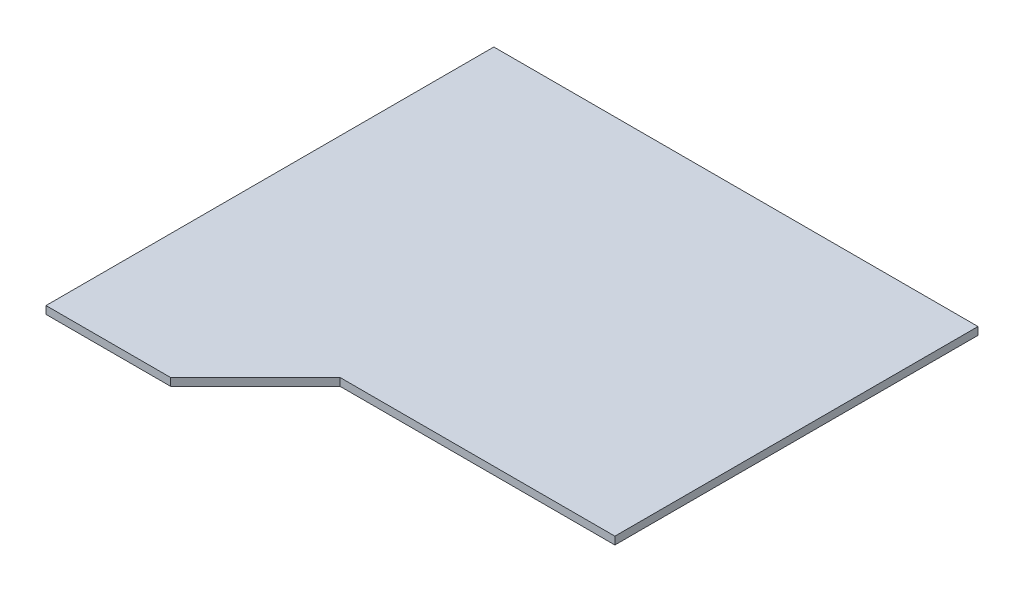
SolidWorks part; units mm, degrees
ref_plane "Front Plane" through (0, 0, 0) normal (0, 0, 1) x (1, 0, 0)
ref_plane "Top Plane" through (0, 0, 0) normal (0, 1, 0) x (1, 0, 0)
ref_plane "Right Plane" through (0, 0, 0) normal (1, 0, 0) x (0, 0, -1)
sketch "Sketch1" plane through (0, 0, 0) normal (0, 1, 0) x (1, 0, 0)
  line L0 (100, 17.5) -> (0, 17.5) construction
  line L1 (0, 0) -> (100, 0) construction
  line L2 (0, 0) -> (0, 92.5) construction
  line L3 (0, 92.5) -> (100, 92.5) construction
  line L4 (100, 0) -> (100, 92.5) construction
  line L5 (25.75, 0) -> (25.75, 92.5) construction
  line L6 (43.25, 0) -> (43.25, 92.5) construction
  line L7 (0, 0) -> (25.75, 0)
  line L8 (25.75, 0) -> (43.25, 17.5)
  line L9 (43.25, 17.5) -> (100, 17.5)
  line L10 (100, 17.5) -> (100, 92.5)
  line L11 (100, 92.5) -> (0, 92.5)
  line L12 (0, 92.5) -> (0, 0)
extrude "Boss-Extrude1" add sketch "Sketch1" along normal blind 1.5875
ref_plane "center-of-slot" through (0, 0.7937, 0) normal (0, 1, 0) x (1, 0, 0)
